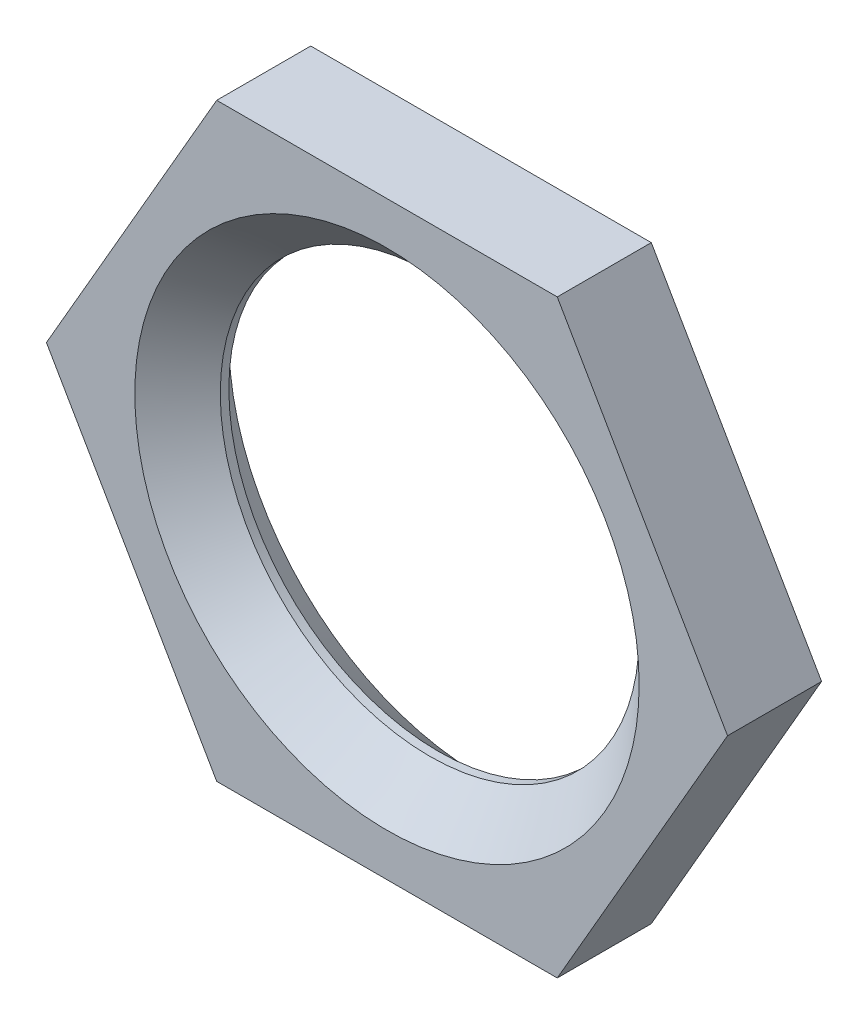
SolidWorks part; units mm, degrees
ref_plane "Front Plane" through (0, 0, 0) normal (0, 0, 1) x (1, 0, 0)
ref_plane "Top Plane" through (0, 0, 0) normal (0, 1, 0) x (1, 0, 0)
ref_plane "Right Plane" through (0, 0, 0) normal (1, 0, 0) x (0, 0, -1)
sketch "Sketch1" plane through (0, 0, 0) normal (0, 0, 1) x (1, 0, 0)
  line L1 (3.9837, 6.9) -> (-3.9837, 6.9)
  line L2 (-3.9837, 6.9) -> (-7.9674, 0)
  line L3 (-7.9674, 0) -> (-3.9837, -6.9)
  line L4 (-3.9837, -6.9) -> (3.9837, -6.9)
  line L5 (3.9837, -6.9) -> (7.9674, 0)
  line L6 (7.9674, 0) -> (3.9837, 6.9)
  circle A0 centre (0, 0) radius 6.9 construction
  circle A1 centre (0, 0) radius 4.9
  point P1 (0, 6.9)
  dimension "D2" = 9.8
  dimension "D1" = 13.8
extrude "Boss-Extrude1" add sketch "Sketch1" along normal blind 2.2
chamfer "Chamfer1" distance 1 angle 45 2 edges at (4.9, 0, 0) (4.9, 0, 2.2)
